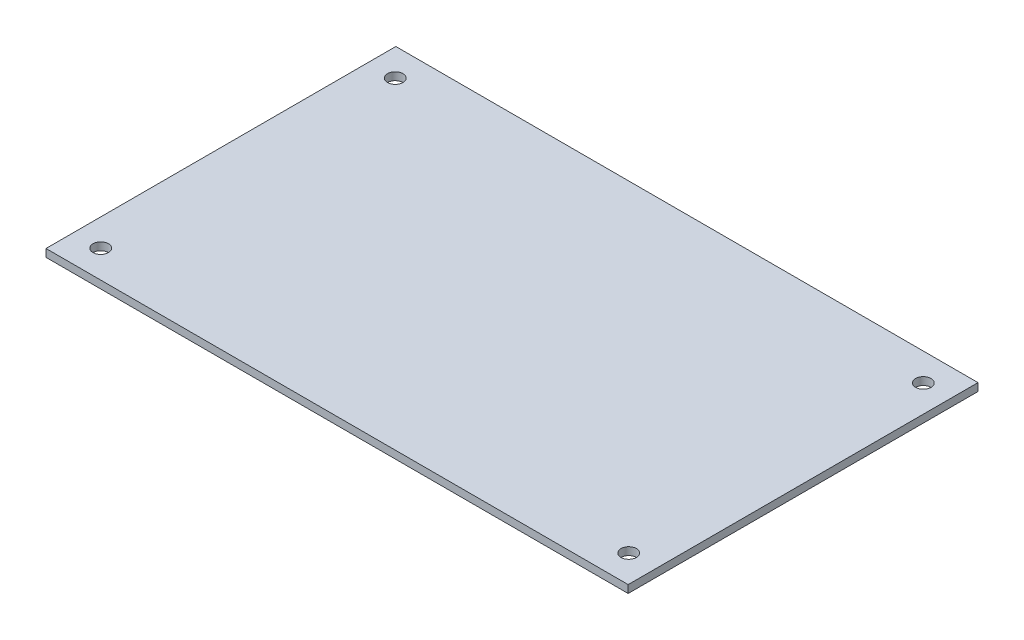
SolidWorks part; units mm, degrees
ref_plane "Front Plane" through (0, 0, 0) normal (0, 0, 1) x (1, 0, 0)
ref_plane "Top Plane" through (0, 0, 0) normal (0, 1, 0) x (1, 0, 0)
ref_plane "Right Plane" through (0, 0, 0) normal (1, 0, 0) x (0, 0, -1)
sketch "Sketch1" plane through (0, 0, 0) normal (0, 1, 0) x (1, 0, 0)
  line L1 (-75.3, 45.25) -> (75.3, 45.25)
  line L2 (-75.3, 45.25) -> (-75.3, -45.25)
  line L3 (-75.3, -45.25) -> (75.3, -45.25)
  line L4 (75.3, 45.25) -> (75.3, -45.25)
  line L5 (-75.3, 45.25) -> (75.3, -45.25) construction
  line L6 (-75.3, -45.25) -> (75.3, 45.25) construction
  line L7 (-68.3, 38.1) -> (68.3, 38.1) construction
  line L8 (-68.3, 38.1) -> (-68.3, -38.1) construction
  line L9 (-68.3, -38.1) -> (68.3, -38.1) construction
  line L10 (68.3, 38.1) -> (68.3, -38.1) construction
  line L11 (-68.3, 38.1) -> (68.3, -38.1) construction
  line L12 (-68.3, -38.1) -> (68.3, 38.1) construction
  circle A0 centre (-68.3, 38.1) radius 2
  circle A1 centre (-68.3, -38.1) radius 2
  circle A2 centre (68.3, 38.1) radius 2
  circle A3 centre (68.3, -38.1) radius 2
  point P0 (0, 0)
  point P6 (0, 0)
  dimension "D5" = 4
  dimension "D1" = 90.5
  dimension "D2" = 150.6
  dimension "D3" = 76.2
  dimension "D4" = 7
extrude "Boss-Extrude1" add sketch "Sketch1" along normal blind 2
